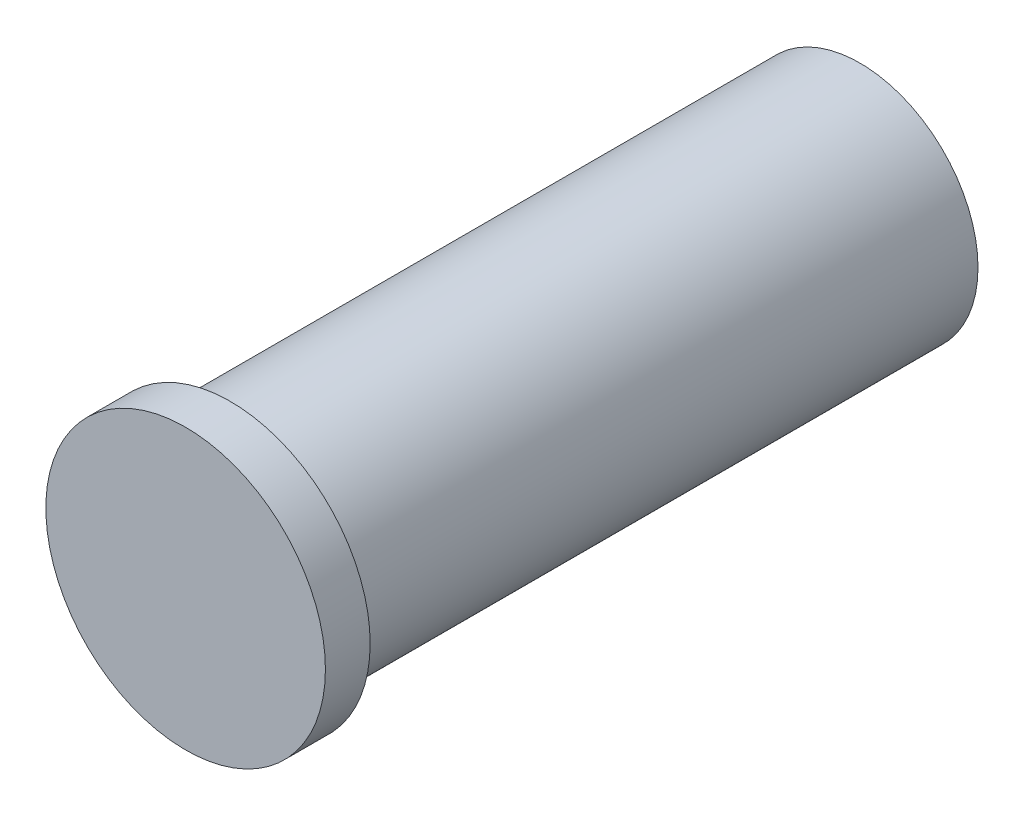
SolidWorks part; units mm, degrees
material "Ti-6Al-2Sn-2Zr-2Mo-2Cr-0.25Si (SS)"
ref_plane "Front Plane" through (0, 0, 0) normal (0, 0, 1) x (1, 0, 0)
ref_plane "Top Plane" through (0, 0, 0) normal (0, 1, 0) x (1, 0, 0)
ref_plane "Right Plane" through (0, 0, 0) normal (1, 0, 0) x (0, 0, -1)
sketch "Sketch1" plane through (0, 0, 0) normal (0, 0, 1) x (1, 0, 0)
  circle A0 centre (0, 0) radius 27
  circle A1 centre (0, 0) radius 30
  dimension "D1" = 60
  dimension "D2" = 54
extrude "Boss-Extrude1" add sketch "Sketch1" along normal blind 160
scale "Scale1" scale about origin uniform scaling yes scale factor 0.703704
ref_plane "Plane1" through (0, 0, 112.5926) normal (0, 0, 1) x (1, 0, 0)
sketch "Sketch3" plane through (0, 0, 112.5926) normal (0, 0, 1) x (1, 0, 0)
  circle A1 centre (0, 0) radius 25
  dimension "D1" = 50
extrude "Boss-Extrude4" add sketch "Sketch3" along normal blind 8
